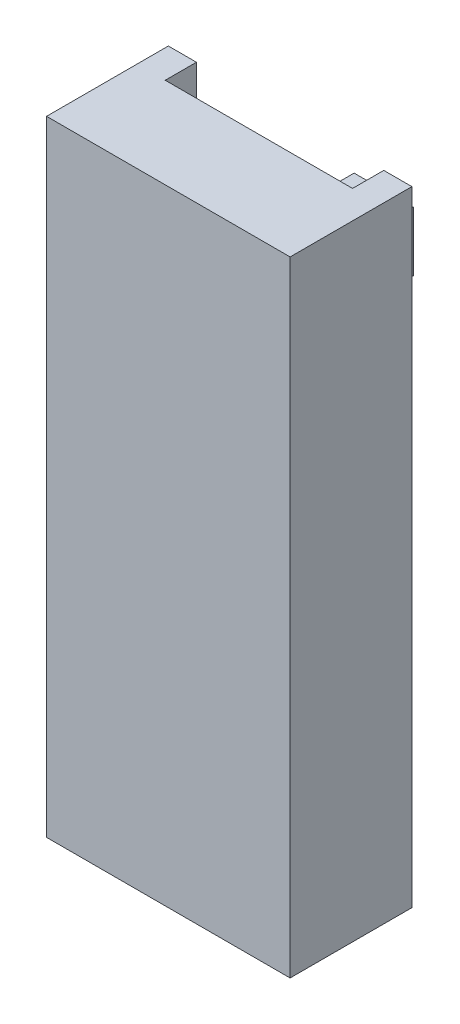
SolidWorks part; units mm, degrees
ref_plane "Front Plane" through (0, 0, 0) normal (0, 0, 1) x (1, 0, 0)
ref_plane "Top Plane" through (0, 0, 0) normal (0, 1, 0) x (1, 0, 0)
ref_plane "Right Plane" through (0, 0, 0) normal (1, 0, 0) x (0, 0, -1)
sketch "Sketch1" plane through (0, 0, 0) normal (0, 1, 0) x (1, 0, 0)
  line L1 (-2.6387, 2.1975) -> (5.1613, 2.1975)
  line L2 (-2.6387, 2.1975) -> (-2.6387, -1.7025)
  line L3 (-2.6387, -1.7025) -> (5.1613, -1.7025)
  line L4 (5.1613, 2.1975) -> (5.1613, -1.7025)
  dimension "D1" = 7.8
  dimension "D2" = 3.9
extrude "Boss-Extrude1" add sketch "Sketch1" along normal blind 20
sketch "Sketch3" plane through (0, 0, 0) normal (0, -1, 0) x (1, 0, 0)
  line L0 (4.2613, -2.1975) -> (-0.2387, -2.1975)
  line L1 (5.1613, -2.1975) -> (-2.6387, -2.1975) construction
  line L2 (-0.2387, -2.1975) -> (-1.7387, -2.1975)
  line L3 (-1.7387, -2.1975) -> (-1.7387, -1.4475)
  line L4 (-1.7387, -1.4475) -> (4.2613, -1.4475)
  line L5 (4.2613, -1.4475) -> (4.2613, -2.1975)
  arc A0 (-0.2387, -2.1975) -> (2.7613, -2.1975) centre (1.2613, -2.1975) cw
  point P12 (-1.5174, -2.1975)
  line M4 (-2.6387, -2.1975) -> (5.1613, -2.1975)
  dimension "D1" = 1.5
  dimension "D2" = 3.9
  dimension "D3" = 6
  dimension "D4" = 0.75
  dimension "D5" = 3
extrude "Cut-Extrude1" cut sketch "Sketch3" against normal blind 15 contours A0 L4 M4 | L4 A0 L0 L5 | A0 L4 | A0 L4 L3 M4
sketch "Sketch4" plane through (0, 20, 0) normal (0, 1, 0) x (1, 0, 0)
  line L0 (5.1613, 2.1975) -> (-2.6387, 2.1975) construction
  line L1 (4.2613, 2.1975) -> (-1.7387, 2.1975)
  line L2 (4.2613, 2.1975) -> (4.2613, 1.1975)
  line L3 (4.2613, 1.1975) -> (-1.7387, 1.1975)
  line L4 (-1.7387, 2.1975) -> (-1.7387, 1.1975)
  line L5 (-2.6387, 2.1975) -> (-2.6387, -1.7025) construction
  dimension "D1" = 6
  dimension "D2" = 0.9
  dimension "D3" = 1
extrude "Cut-Extrude2" cut sketch "Sketch4" against normal blind 2
sketch "Sketch6" plane through (0, 0, -2.1975) normal (0, 0, -1) x (-1, 0, 0)
  line L0 (1.7387, 15) -> (-4.2613, 15) construction
  line L1 (-3.2113, 17.45) -> (-1.3113, 17.45)
  line L2 (-3.2113, 17.45) -> (-3.2113, 15.55)
  line L3 (-3.2113, 15.55) -> (-1.3113, 15.55)
  line L4 (-1.3113, 17.45) -> (-1.3113, 15.55)
  line L5 (-4.2613, 18) -> (1.7387, 18) construction
  line L6 (-4.2613, 18) -> (-4.2613, 20) construction
  dimension "D1" = 0.55
  dimension "D2" = 0.55
  dimension "D3" = 1.05
  dimension "D4" = 1.9
extrude "Boss-Extrude3" add sketch "Sketch6" along normal blind 2
sketch "Sketch7" plane through (0, 0, -2.1975) normal (0, 0, -1) x (-1, 0, 0)
  line L1 (-1.2613, 17.5) -> (0.7387, 17.5)
  line L2 (-1.2613, 17.5) -> (-1.2613, 15.5)
  line L3 (-1.2613, 15.5) -> (0.7387, 15.5)
  line L4 (0.7387, 17.5) -> (0.7387, 15.5)
  line L6 (1.7387, 15) -> (-4.2613, 15) construction
  line L7 (2.6387, 20) -> (2.6387, 0) construction
  dimension "D1" = 2
  dimension "D2" = 2
  dimension "D3" = 0.5
  dimension "D4" = 1.9
extrude "Cut-Extrude3" cut sketch "Sketch7" against normal blind 2
